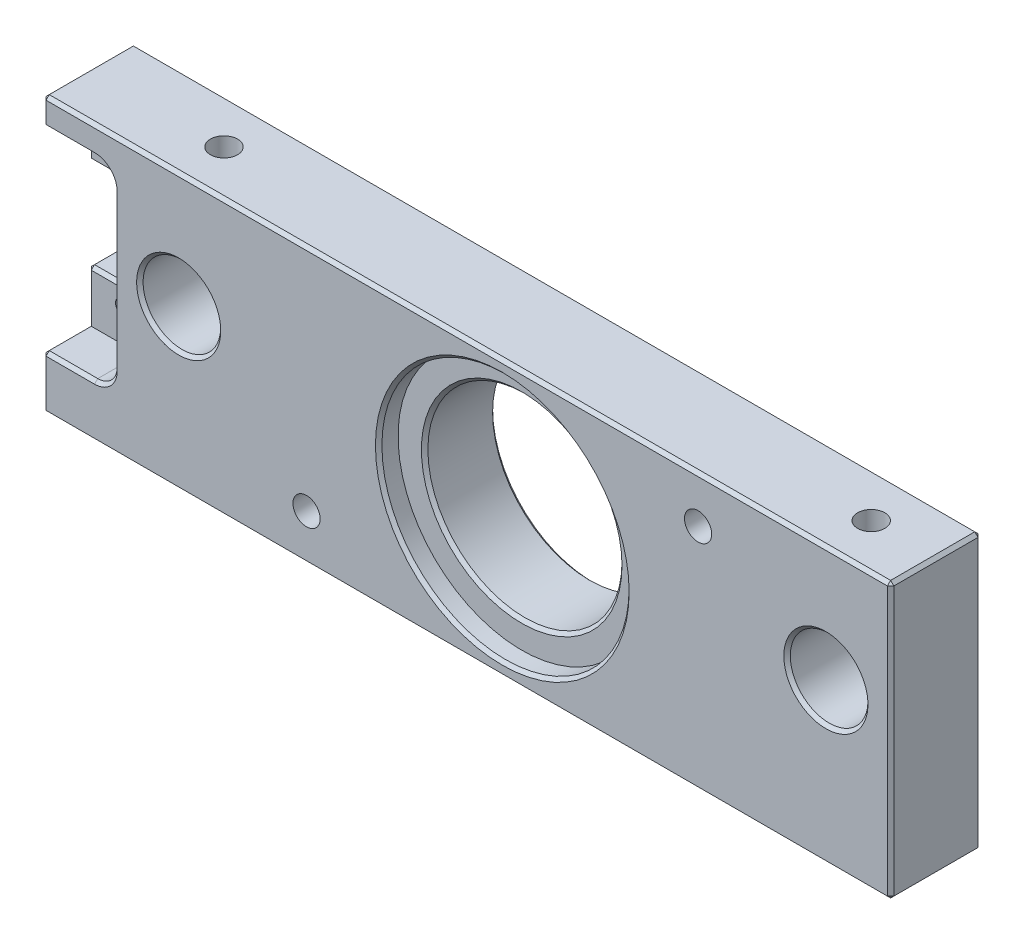
SolidWorks part; units mm, degrees
ref_plane "Front Plane" through (0, 0, 0) normal (0, 0, 1) x (1, 0, 0)
ref_plane "Top Plane" through (0, 0, 0) normal (0, 1, 0) x (1, 0, 0)
ref_plane "Right Plane" through (0, 0, 0) normal (1, 0, 0) x (0, 0, -1)
sketch "Sketch1" plane through (0, 0, 0) normal (0, 0, 1) x (1, 0, 0)
  line L1 (-60, -21.25) -> (60, -21.25)
  line L2 (-60, -21.25) -> (-60, 21.25)
  line L3 (-60, 21.25) -> (60, 21.25)
  line L4 (60, -21.25) -> (60, 21.25)
  line L5 (-60, -21.25) -> (60, 21.25) construction
  line L6 (-60, 21.25) -> (60, -21.25) construction
  point P0 (0, 0)
  dimension "D1" = 120
  dimension "D2" = 42.5
extrude "Boss-Extrude1" add sketch "Sketch1" along normal mid plane 14
sketch "Sketch2" plane through (0, 0, 7) normal (0, 0, 1) x (1, 0, 0)
  circle A0 centre (0, 0) radius 19.1
  dimension "D1" = 38.2
extrude "Cut-Extrude1" cut sketch "Sketch2" against normal blind 3
sketch "Sketch3" plane through (0, 0, 4) normal (0, 0, 1) x (1, 0, 0)
  circle A0 centre (0, 0) radius 15
extrude "Cut-Extrude2" cut sketch "Sketch3" against normal through all
hole_wizard "M5x0.8 Tapped Hole3" positions "Sketch13" profile "Sketch12" tap size "M5x0.8" standard "ANSI Metric"
sketch "Sketch13" plane through (0, 0, 7) normal (0, 0, 1) x (1, 0, 0)
  line L0 (-906.3078, -422.6183) -> (44409.0816, 20708.2948) construction
  line L1 (-1000, 0) -> (49000, 0) construction
  circle A0 centre (0, 0) radius 33.375 construction
  point P0 (-30.248, -14.1049)
  point P2 (30.248, 14.1049)
  dimension "D3" = 66.75
  dimension "D1" = 25
sketch "Sketch12" plane through (-30.248, -14.1049, 7) normal (1, 0, 0) x (0, -1, 0)
  line L0 (0, 0) -> (0, 15.2618)
  line L1 (0, 15.2618) -> (2.1, 14)
  line L2 (2.1, 14) -> (2.1, 0)
  line L5 (2.1, 0) -> (0, 0)
  line L10 (0, 15.2618) -> (-2.1, 14) construction
  line L11 (0, -6.35) -> (0, 107.95) construction
  dimension "Tap Drill Dia." = 4.2
  dimension "Tap Drill Depth" = 14
  dimension "Drill Angle" = 118
cosmetic thread "Hole Thread6" parameters "D1"=10, "D2"=5
cosmetic thread "Hole Thread7" parameters "D1"=10, "D2"=5
sketch "Sketch5" plane through (0, 0, 7) normal (0, 0, 1) x (1, 0, 0)
  line L0 (-40.6477, 3.4) -> (36.4799, 3.4) construction
  circle A0 centre (-50, 3.4) radius 6
  circle A1 centre (50, 3.4) radius 6
  dimension "D1" = 12
  dimension "D2" = 12
  dimension "D4" = 50
  dimension "D3" = 50
  dimension "D5" = 3.4
extrude "Cut-Extrude4" cut sketch "Sketch5" against normal through all
hole_wizard "M5x0.8 Tapped Hole2" positions "Sketch11" profile "Sketch10" tap size "M5x0.8" standard "ANSI Metric"
sketch "Sketch11" plane through (0, -21.25, 0) normal (0, -1, 0) x (-1, 0, 0)
  line L0 (-1000, 0) -> (49000, 0) construction
  point P0 (50, 0)
  point P4 (22, 0)
  dimension "D1" = 22
  dimension "D2" = 50
sketch "Sketch10" plane through (-50, -21.25, 0) normal (1, 0, 0) x (0, 0, -1)
  line L0 (0, 0) -> (0, 15.2618)
  line L1 (0, 15.2618) -> (2.1, 14)
  line L2 (2.1, 14) -> (2.1, 0)
  line L5 (2.1, 0) -> (0, 0)
  line L10 (0, 15.2618) -> (-2.1, 14) construction
  line L11 (0, -6.35) -> (0, 107.95) construction
  dimension "Tap Drill Dia." = 4.2
  dimension "Tap Drill Depth" = 14
  dimension "Drill Angle" = 118
cosmetic thread "Hole Thread3" parameters "D1"=10, "D2"=5
cosmetic thread "Hole Thread5" parameters "D1"=10, "D2"=5
sketch "Sketch6" plane through (0, -21.25, 0) normal (0, -1, 0) x (1, 0, 0)
  line L0 (-60, 0) -> (60, 0) construction
  line L1 (-60, 7) -> (-60, -7) construction
  line L2 (60, 7) -> (60, -7) construction
  circle A4 centre (-36, 0) radius 1.25
  dimension "D9" = 2.5
  dimension "D11" = 24
extrude "Cut-Extrude5" cut sketch "Sketch6" against normal blind 10
mirror "Mirror1" about plane through (0, 0, 0) normal (1, 0, 0) of "Cut-Extrude5", "M5x0.8 Tapped Hole2"
hole_wizard "M5x0.8 Tapped Hole1" positions "Sketch9" profile "Sketch8" tap size "M5x0.8" standard "ANSI Metric"
sketch "Sketch9" plane through (0, 21.25, 0) normal (0, 1, 0) x (1, 0, 0)
  line L0 (-1000, 0) -> (49000, 0) construction
  line L1 (-60, -7) -> (-60, 7) construction
  line L2 (60, -7) -> (60, 7) construction
  point P0 (-50, 0)
  point P3 (50, 0)
  dimension "D1" = 10
  dimension "D2" = 10
sketch "Sketch8" plane through (-50, 21.25, 0) normal (1, 0, 0) x (0, 0, 1)
  line L0 (0, 0) -> (0, 11.85)
  line L1 (0, 11.85) -> (2.1, 11.85)
  line L2 (2.1, 11.85) -> (2.1, 0)
  line L5 (2.1, 0) -> (0, 0)
  line L11 (0, -6.35) -> (0, 107.95) construction
  dimension "Thru Tap Drill Dia." = 4.2
  dimension "Thru Tap Drill Depth" = 11.85
cosmetic thread "Hole Thread1" parameters "D2"=5
cosmetic thread "Hole Thread2" parameters "D2"=5
sketch "Sketch16" plane through (-60, 0, 0) normal (-1, 0, 0) x (0, 0, 1)
  line L1 (-7, -21.25) -> (7, -21.25)
  line L2 (-7, -21.25) -> (-7, 21.25)
  line L3 (-7, 21.25) -> (7, 21.25)
  line L4 (7, -21.25) -> (7, 21.25)
  line L5 (-7, -21.25) -> (7, 21.25) construction
  line L6 (-7, 21.25) -> (7, -21.25) construction
  point P0 (0, 0)
extrude "Boss-Extrude2" add sketch "Sketch16" along normal blind 11
hole_wizard "M2x0.4 Tapped Hole1" [suppressed] positions "Sketch15" profile "Sketch14" tap size "M2x0.4" standard "ANSI Metric"
sketch "Sketch15" plane through (0, 21.25, 0) normal (0, 1, 0) x (1, 0, 0)
  point P0 (-33.5, 0)
  point P2 (-40, 0)
  dimension "D1" = 40
  dimension "D2" = 33.5
sketch "Sketch14" plane through (-33.5, 21.25, 0) normal (1, 0, 0) x (0, 0, 1)
  line L0 (0, 0) -> (0, 6.4807)
  line L1 (0, 6.4807) -> (0.8, 6)
  line L2 (0.8, 6) -> (0.8, 0)
  line L5 (0.8, 0) -> (0, 0)
  line L10 (0, 6.4807) -> (-0.8, 6) construction
  line L11 (0, -6.35) -> (0, 107.95) construction
  dimension "Tap Drill Dia." = 1.6
  dimension "Tap Drill Depth" = 6
  dimension "Drill Angle" = 118
cosmetic thread "Hole Thread8" [suppressed] parameters "D1"=4, "D2"=2
cosmetic thread "Hole Thread9" [suppressed] parameters "D1"=4, "D2"=2
sketch "Sketch17" plane through (0, 0, 7) normal (0, 0, 1) x (1, 0, 0)
  line L0 (-71, -21.25) -> (-71, 21.25) construction
  line L1 (-60, -13) -> (-71, -13)
  line L2 (-60, -13) -> (-60, 17)
  line L3 (-60, 17) -> (-71, 17)
  line L4 (-71, -13) -> (-71, 17)
  line L5 (-60, -13) -> (-71, 17) construction
  line L6 (-60, 17) -> (-71, -13) construction
  point P0 (-65.5, 2)
  dimension "D1" = 30
  dimension "D2" = 11
  dimension "D3" = 17
extrude "Cut-Extrude6" cut sketch "Sketch17" against normal blind 7
hole_wizard "M3x0.5 Tapped Hole1" positions "Sketch20" profile "Sketch19" tap size "M3x0.5" standard "ANSI Metric" end condition through all
sketch "Sketch20" plane through (0, 0, 0) normal (0, 0, 1) x (1, 0, 0)
  line L0 (-65.5, -8) -> (-65.5, 12)
  line L1 (-71, 17) -> (-71, -13) construction
  line L2 (-60, 17) -> (-71, 17) construction
  point P0 (-65.5, 12)
  point P2 (-65.5, -8)
  dimension "D1" = 5
  dimension "D2" = 20
  dimension "D3" = 5.5
cosmetic thread "Hole Thread10" parameters "D2"=3
cosmetic thread "Hole Thread11" parameters "D2"=3
sketch "Sketch19" plane through (-65.5, 12, 0) normal (1, 0, 0) x (0, -1, 0)
  line L0 (0, 0) -> (0, 7)
  line L1 (0, 7) -> (1.25, 7)
  line L2 (1.25, 7) -> (1.25, 0)
  line L5 (1.25, 0) -> (0, 0)
  line L11 (0, -6.35) -> (0, 107.95) construction
  dimension "Thru Tap Drill Dia." = 2.5
  dimension "Thru Tap Drill Depth" = 7
sketch "Sketch21" plane through (0, 0, 0) normal (0, 0, 1) x (1, 0, 0)
  line L0 (-71, 17) -> (-71, -13) construction
  line L1 (-71, 9) -> (-61, 9)
  line L2 (-71, 9) -> (-71, -5)
  line L3 (-71, -5) -> (-61, -5)
  line L4 (-61, 9) -> (-61, -5)
  line L6 (-60, 2) -> (-71, 2) construction
  line L7 (-60, -13) -> (-60, 17) construction
  dimension "D1" = 14
  dimension "D2" = 7
  dimension "D3" = 10
extrude "Cut-Extrude7" cut sketch "Sketch21" against normal through all
fillet "Fillet1" radius 3 4 edges at (-60, -13, 3.5) (-60, 17, 3.5) (-61, -5, -3.5) (-61, 9, -3.5)
chamfer "Chamfer1" distance 0.5 angle 45 44 edges at (-44, 3.4, -7) (56, 3.4, -7) (56, 3.4, 7) (-44, 3.4, 7) (15, 0, -7) (15, 0, 4) (19.1, 0, 7) (-36, -21.25, -1.25) (36, -21.25, -1.25) (-5.5, -21.25, -7) (60, -21.25, 0) (60, 0, -7) (60, 21.25, 0) (60, 0, 7) (-5.5, -21.25, 7) (-5.5, 21.25, -7) (-5.5, 21.25, 7) (-67.5, 9, -7) (-61.8787, 8.1213, -7) (-61, 2, -7) (-61.8787, -4.1213, -7) (-67.5, -5, -7) (-61.8787, -4.1213, 0) (-61, 2, 0) (-61.8787, 8.1213, 0) (-67.5, 9, 0) (-71, 17, 3.5) (-71, 13, 0) (-71, 19.125, 7) (-67, 17, 7) (-60.8787, 16.1213, 7) (-60, 2, 7) (-60.8787, -12.1213, 7) (-67, -13, 7) (-71, 9, -3.5) (-71, -5, -3.5) (-71, -9, 0) (-71, -13, 3.5) (-71, -17.125, 7) (-71, -21.25, 0) (-71, -13.125, -7) (-71, 21.25, 0) (-71, 15.125, -7) (-67.5, -5, 0)
equation "\"D2@Sketch21\" = \"D1@Sketch21\" / 2"
